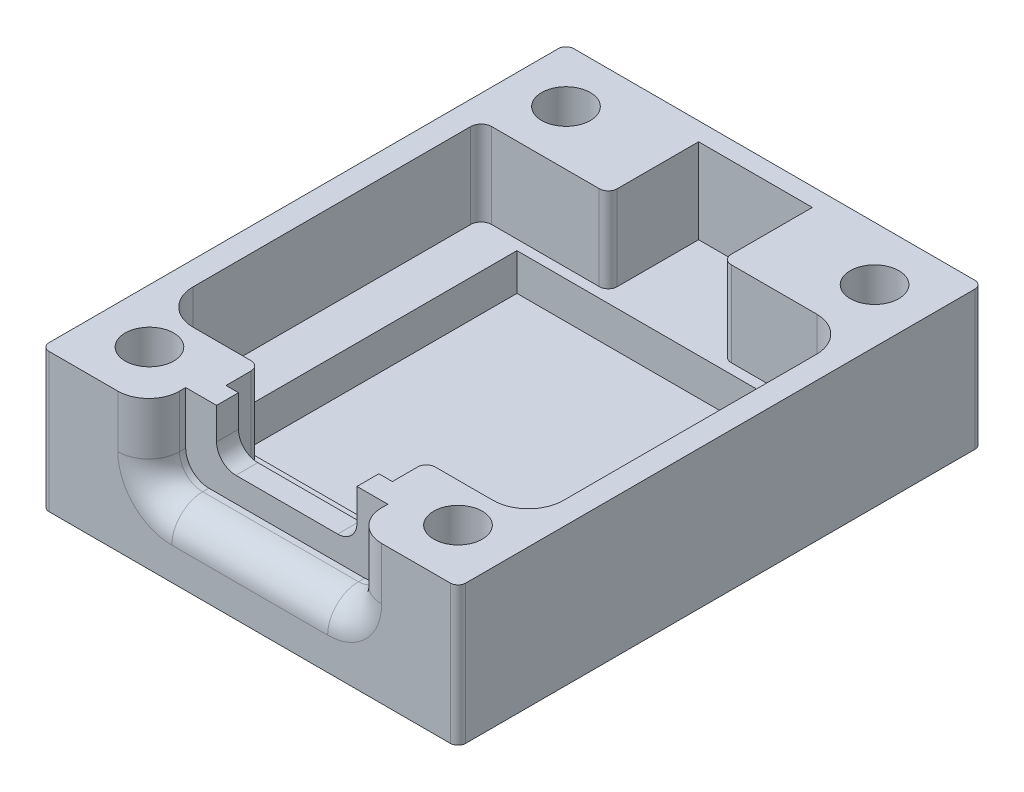
SolidWorks part; units mm, degrees
ref_plane "前视基准面" through (0, 0, 0) normal (0, 0, 1) x (1, 0, 0)
ref_plane "上视基准面" through (0, 0, 0) normal (0, 1, 0) x (1, 0, 0)
ref_plane "右视基准面" through (0, 0, 0) normal (1, 0, 0) x (0, 0, -1)
sketch "草图1" plane through (0, 0, 0) normal (0, 1, 0) x (1, 0, 0)
  line L1 (-13.5, -17) -> (13.5, -17)
  line L2 (-13.5, -17) -> (-13.5, 17)
  line L3 (-13.5, 17) -> (13.5, 17)
  line L4 (13.5, -17) -> (13.5, 17)
  line L5 (-13.5, -17) -> (13.5, 17) construction
  line L6 (-13.5, 17) -> (13.5, -17) construction
  point P0 (0, 0)
  dimension "D1" = 27
  dimension "D2" = 34
extrude "凸台-拉伸1" add sketch "草图1" along normal blind 9
sketch "草图3" plane through (0, 9, 0) normal (0, 1, 0) x (1, 0, 0)
  line L0 (3.399, 15.5693) -> (3.399, 10.5552) construction
  line L1 (4.2441, 9.7242) -> (9.7813, 9.7242) construction
  line L2 (-3.475, 15.5693) -> (-3.475, 10.545) construction
  line L3 (-11.3052, 9.7173) -> (-4.322, 9.7173) construction
  line L4 (-11.7159, 9.2832) -> (-11.7159, -8.6982) construction
  line L5 (-9.6839, -10.7252) -> (-5.9398, -10.7252) construction
  line L6 (-5.1119, -11.5584) -> (-5.1119, -12.93) construction
  line L7 (5.1751, -11.5457) -> (5.1751, -12.93) construction
  line L8 (5.9857, -10.7224) -> (9.7322, -10.7224) construction
  line L9 (11.7777, 7.699) -> (11.7777, -8.684) construction
  line L10 (-5.1119, -12.93) -> (5.1751, -12.93) construction
  line L11 (-3.475, 15.5693) -> (3.399, 15.5693) construction
  line L12 (-0.038, 15.5693) -> (0.0316, -12.93) construction
  line L13 (-0.0032, 1.3197) -> (6.2202, 1.3197) construction
  line L14 (-13.5, -17) -> (13.5, -17) construction
  line L15 (-3.725, 15.8193) -> (3.649, 15.8193)
  line L16 (3.649, 15.8193) -> (3.649, 10.5547)
  line L17 (4.2412, 9.9742) -> (9.7834, 9.9742)
  line L18 (12.0277, 7.6994) -> (12.0277, -8.6836)
  line L19 (5.9885, -10.9724) -> (9.7314, -10.9724)
  line L20 (5.4251, -11.5464) -> (5.4251, -13.18)
  line L21 (-5.3619, -13.18) -> (5.4251, -13.18)
  line L22 (-5.3619, -11.5575) -> (-5.3619, -13.18)
  line L23 (-9.6839, -10.9752) -> (-5.9398, -10.9752)
  line L24 (-11.9659, 9.2829) -> (-11.9659, -8.6985)
  line L25 (-11.311, 9.9673) -> (-4.3189, 9.9673)
  line L26 (-3.725, 15.8193) -> (-3.725, 10.545)
  arc A0 (3.649, 10.5547) -> (4.2412, 9.9742) centre (4.2269, 10.552) ccw
  arc A1 (12.0277, 7.6994) -> (9.7834, 9.9742) centre (9.7457, 7.6925) ccw
  arc A2 (9.7314, -10.9724) -> (12.0277, -8.6836) centre (9.7457, -8.6905) ccw
  arc A3 (5.9885, -10.9724) -> (5.4251, -11.5464) centre (6.003, -11.5502) ccw
  arc A4 (-5.3619, -11.5575) -> (-5.9398, -10.9752) centre (-5.9398, -11.5532) ccw
  arc A5 (-11.9659, -8.6985) -> (-9.6839, -10.9752) centre (-9.6839, -8.6932) ccw
  arc A6 (-11.311, 9.9673) -> (-11.9659, 9.2829) centre (-11.2823, 9.2842) ccw
  arc A7 (-4.3189, 9.9673) -> (-3.725, 10.545) centre (-4.303, 10.545) ccw
  arc A8 (-11.9659, -8.6985) -> (-9.6839, -10.9752) centre (-9.6839, -8.6932) ccw construction
  arc A9 (-11.311, 9.9673) -> (-11.9659, 9.2829) centre (-11.2823, 9.2842) ccw construction
  arc A24 (3.399, 10.5552) -> (4.2441, 9.7242) centre (4.2269, 10.552) ccw construction
  arc A27 (-4.322, 9.7173) -> (-3.475, 10.545) centre (-4.303, 10.545) ccw construction
  arc A30 (-5.1119, -11.5584) -> (-5.9398, -10.7252) centre (-5.9398, -11.5532) ccw construction
  arc A33 (5.9857, -10.7224) -> (5.1751, -11.5457) centre (6.003, -11.5502) ccw construction
  arc A36 (9.7322, -10.7224) -> (11.7777, -8.684) centre (9.7457, -8.6905) ccw construction
  arc A39 (-11.7159, -8.6982) -> (-9.6839, -10.7252) centre (-9.6839, -8.6932) ccw construction
  arc A42 (-11.3052, 9.7173) -> (-11.7159, 9.2832) centre (-11.2823, 9.2842) ccw construction
  arc A45 (11.7777, 7.699) -> (9.7813, 9.7242) centre (9.7457, 7.6925) ccw construction
  point P2 (0, 0)
  point P9 (0, 0)
  point P10 (0, 0)
  point P13 (0, 0)
  point P14 (0, 0)
  point P50 (0, 0)
  point P54 (-11.2823, 9.2842)
  point P55 (-5.9398, -10.7252)
  point P62 (0, 0)
  point P66 (3.599, 15.7693)
  point P67 (0, 0)
  dimension "D1" = 2.032
  dimension "D3" = 2.032
  dimension "D5" = 0.8279
  dimension "D9" = 0.8279
  dimension "D11" = 2.032
  dimension "D13" = 0.4336
  dimension "D15" = 0.8279
  dimension "D19" = 0.8279
  dimension "D2" = 16.383
  dimension "D4" = 3.7465
  dimension "D6" = 1.3843
  dimension "D7" = 10.287
  dimension "D8" = 1.3716
  dimension "D10" = 3.7441
  dimension "D12" = 17.9814
  dimension "D14" = 6.9832
  dimension "D16" = 5.0243
  dimension "D17" = 6.874
  dimension "D18" = 5.0141
  dimension "D20" = 5.5372
  dimension "D21" = 4.07
  dimension "D22" = 9.7644
  dimension "D23" = 11.2596
  dimension "D24" = 9.7051
  dimension "D25" = 9.7244
  dimension "D26" = 6.3729
  dimension "D27" = 10.0101
  dimension "D28" = 10.0129
  dimension "D29" = 7.9646
  dimension "D30" = 0.8279
  dimension "D31" = 0.8279
  dimension "D32" = 0.8279
  dimension "D33" = 0.8279
  dimension "D34" = 23.4936
  dimension "D35" = 20.4466
  dimension "D36" = 0.25
extrude "切除-拉伸1" cut sketch "草图3" against normal blind 5.5
sketch "草图5" plane through (0, 3.5, 0) normal (0, 1, 0) x (1, 0, 0)
  line L1 (-9, -10.6807) -> (9, -10.6807)
  line L2 (-9, -10.6807) -> (-9, 9.3193)
  line L3 (-9, 9.3193) -> (9, 9.3193)
  line L4 (9, -10.6807) -> (9, 9.3193)
  line L5 (-9, -10.6807) -> (9, 9.3193) construction
  line L6 (-9, 9.3193) -> (9, -10.6807) construction
  line L9 (3.649, 15.8193) -> (-3.725, 15.8193) construction
  point P0 (0, -0.6807)
  point P5 (0, -1.0883)
  point P7 (0, -5.0406)
  dimension "D1" = 18
  dimension "D2" = 20
  dimension "D3" = 6.5
extrude "切除-拉伸2" cut sketch "草图5" against normal blind 2.4
sketch "草图7" plane through (0, 0, 17) normal (0, 0, 1) x (1, 0, 0)
  line L0 (0, 0) -> (0, 10.3981) construction
  line L1 (-13.5, 9) -> (13.5, 9) construction
  line L2 (-4.55, 5.7) -> (4.55, 5.7)
  line L3 (-4.55, 5.7) -> (-4.55, 9)
  line L4 (-4.55, 9) -> (4.55, 9)
  line L5 (4.55, 5.7) -> (4.55, 9)
  line L6 (-4.55, 5.7) -> (4.55, 9) construction
  line L7 (-4.55, 9) -> (4.55, 5.7) construction
  point P3 (0, 7.35)
  dimension "D1" = 3.3
  dimension "D2" = 9.1
extrude "切除-拉伸3" cut sketch "草图7" against normal up to surface (3.82 mm away) up to face at (0.0316, 6.25, 13.18)
sketch "草图8" plane through (0, 0, 17) normal (0, 0, 1) x (1, 0, 0)
  line L0 (4.55, 5.7) -> (4.55, 9) construction
  line L1 (-4.55, 5.7) -> (4.55, 5.7) construction
  line L2 (-4.55, 9) -> (-4.55, 5.7) construction
  line L3 (4.55, 5.7) -> (4.55, 9) construction
  line L4 (-4.55, 5.7) -> (4.55, 5.7) construction
  line L5 (-4.55, 9) -> (-4.55, 5.7) construction
  line L11 (6.55, 4.1) -> (-6.55, 4.1)
  line L13 (-4.55, 9) -> (4.55, 9)
  line L14 (4.55, 9) -> (6.55, 9)
  line L15 (4.55, 9) -> (13.5, 9) construction
  line L16 (6.55, 9) -> (6.55, 4.1)
  line L17 (-4.55, 9) -> (-6.55, 9)
  line L18 (-13.5, 9) -> (-4.55, 9) construction
  line L19 (-6.55, 9) -> (-6.55, 4.1)
  point P3 (0, 0)
  dimension "D1" = 2
  dimension "D2" = 2
  dimension "D3" = 1.6
extrude "切除-拉伸4" cut sketch "草图8" against normal blind 2.4
sketch "草图9" plane through (0, 9, 0) normal (0, 1, 0) x (1, 0, 0)
  line L0 (0, 0) -> (13.5, 0) construction
  line L1 (13.5, -17) -> (13.5, 17) construction
  line L2 (0, 0) -> (0, 17) construction
  line L3 (13.5, 17) -> (-13.5, 17) construction
  line L4 (6.55, -17) -> (13.5, -17) construction
  circle A0 centre (-10, 13.5) radius 1.575
  circle A4 centre (10, 13.5) radius 1.575
  circle A5 centre (10, -13.5) radius 1.575
  circle A6 centre (-10, -13.5) radius 1.575
  dimension "D1" = 3.15
  dimension "D2" = 10
  dimension "D3" = 13.5
extrude "切除-拉伸5" cut sketch "草图9" against normal blind 3.1
fillet "圆角1" radius 0.5 4 edges at (13.5, 4.5, -17) (13.5, 4.5, 17) (-13.5, 4.5, -17) (-13.5, 4.5, 17)
fillet "圆角2" radius 1.5 2 edges at (6.55, 4.1, 15.8) (-6.55, 4.1, 15.8)
fillet "圆角3" radius 1.25 2 edges at (-4.55, 5.7, 13.89) (4.55, 5.7, 13.89)
fillet "圆角4" radius 2 5 edges at (-6.55, 7.3, 17) (-6.1107, 4.5393, 17) (6.55, 7.3, 17) (6.1107, 4.5393, 17) (0, 4.1, 17)
